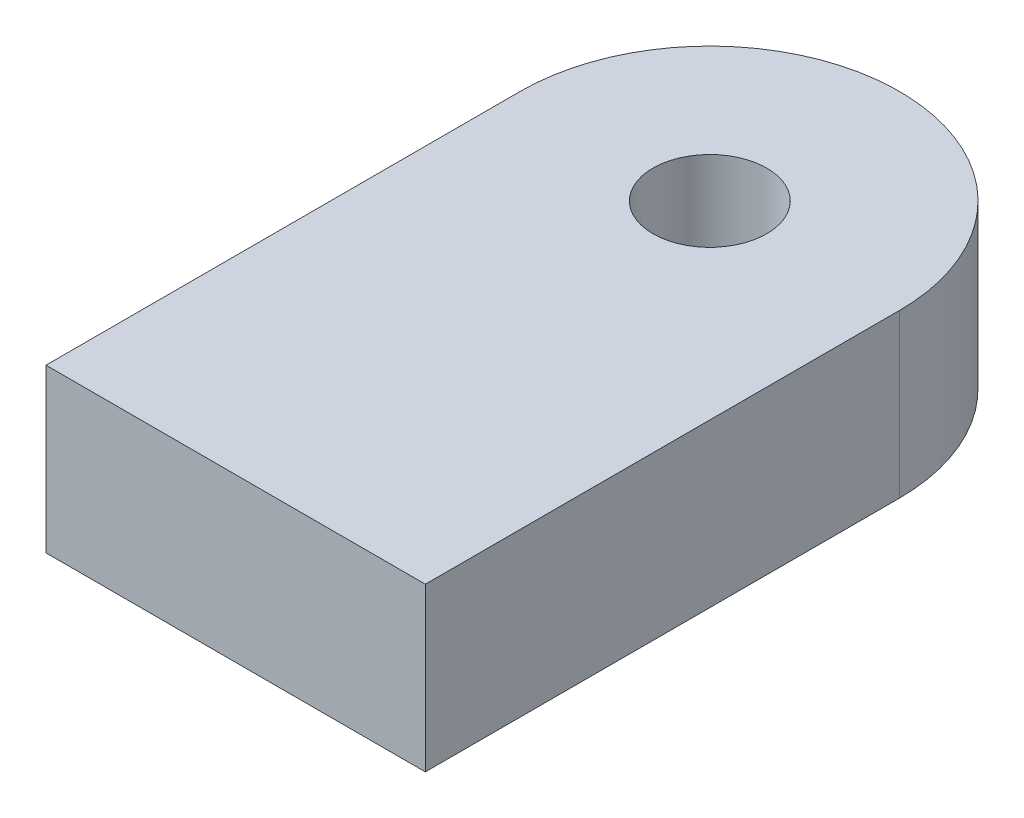
SolidWorks part; units mm, degrees
ref_plane "Front Plane" through (0, 0, 0) normal (0, 0, 1) x (1, 0, 0)
ref_plane "Top Plane" through (0, 0, 0) normal (0, 1, 0) x (1, 0, 0)
ref_plane "Right Plane" through (0, 0, 0) normal (1, 0, 0) x (0, 0, -1)
sketch "Sketch1" plane through (0, 0, 0) normal (0, 1, 0) x (1, 0, 0)
  line L1 (-7, -8.75) -> (7, -8.75)
  line L2 (-7, -8.75) -> (-7, 8.75)
  line L4 (7, -8.75) -> (7, 8.75)
  line L5 (-7, -8.75) -> (7, 8.75) construction
  line L6 (-7, 8.75) -> (7, -8.75) construction
  arc A0 (-7, 8.75) -> (7, 8.75) centre (0, 8.75) cw
  circle A1 centre (0, 8.75) radius 2.1
  point P0 (0, 0)
  dimension "D3" = 4.2
  dimension "D1" = 14
  dimension "D2" = 17.5
extrude "Boss-Extrude1" add sketch "Sketch1" along normal blind 6
